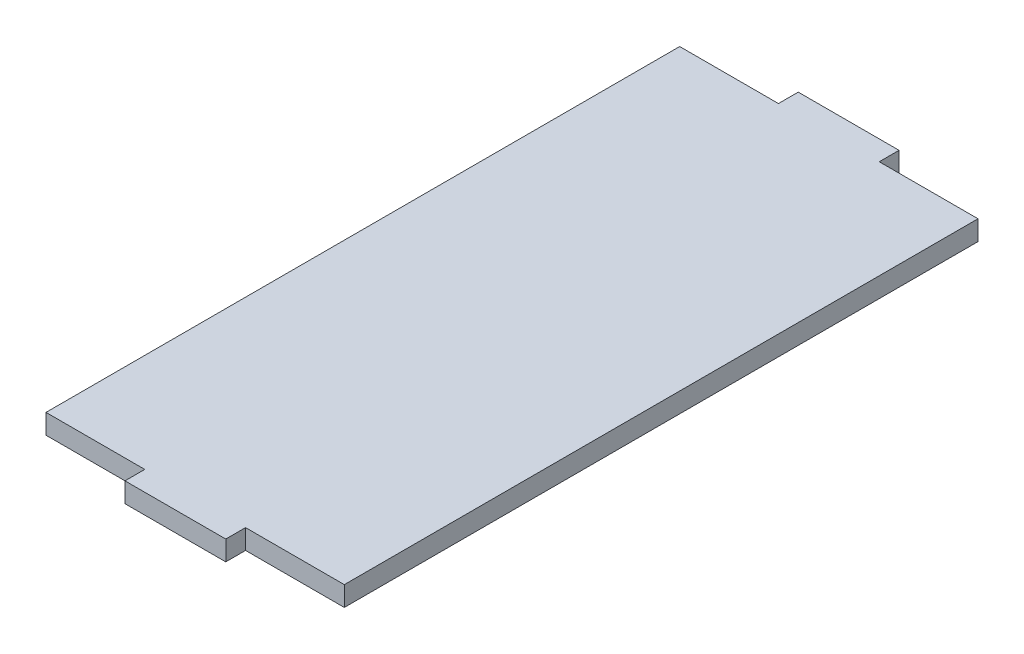
SolidWorks part; units mm, degrees
ref_plane "Front Plane" through (0, 0, 0) normal (0, 0, 1) x (1, 0, 0)
ref_plane "Top Plane" through (0, 0, 0) normal (0, 1, 0) x (1, 0, 0)
ref_plane "Right Plane" through (0, 0, 0) normal (1, 0, 0) x (0, 0, -1)
sketch "Sketch1" plane through (0, 0, 0) normal (0, 1, 0) x (1, 0, 0)
  line L1 (-17.8912, 69.8928) -> (29.9388, 69.8928)
  line L2 (-17.8912, 69.8928) -> (-17.8912, -31.7072)
  line L3 (-17.8912, -31.7072) -> (29.9388, -31.7072)
  line L4 (29.9388, 69.8928) -> (29.9388, -31.7072)
extrude "Boss-Extrude1" add sketch "Sketch1" along normal blind 3.175
sketch "Sketch2" plane through (0, 3.175, 0) normal (0, 1, 0) x (1, 0, 0)
  line L0 (6.0238, 69.8928) -> (6.0238, -31.7072) construction
  line L1 (29.9388, 69.8928) -> (-17.8912, 69.8928) construction
  line L2 (-17.8912, -31.7072) -> (29.9388, -31.7072) construction
  line L3 (-17.8912, 19.0928) -> (29.9388, 19.0928) construction
  line L4 (-2.0562, 69.8928) -> (14.1038, 69.8928)
  line L5 (-2.0562, 69.8928) -> (-2.0562, 73.0678)
  line L6 (-2.0562, 73.0678) -> (14.1038, 73.0678)
  line L7 (14.1038, 69.8928) -> (14.1038, 73.0678)
  line L8 (-17.8912, 69.8928) -> (-17.8912, -31.7072) construction
  line L9 (29.9388, -31.7072) -> (29.9388, 69.8928) construction
  line L10 (14.1038, -31.7072) -> (14.1038, -34.8822)
  line L11 (-2.0562, -34.8822) -> (14.1038, -34.8822)
  line L12 (-2.0562, -31.7072) -> (-2.0562, -34.8822)
  line L13 (-2.0562, -31.7072) -> (14.1038, -31.7072)
  line L14 (6.0238, 73.0678) -> (6.0238, 69.8928) construction
  line L15 (6.0238, -34.8822) -> (6.0238, -31.7072) construction
  dimension "D1" = 16.16
  dimension "D2" = 3.175
  dimension "D3" = 0
extrude "Boss-Extrude2" add sketch "Sketch2" against normal up to surface (3.175 mm away) up to face at (6.0238, 0, -19.0928)
